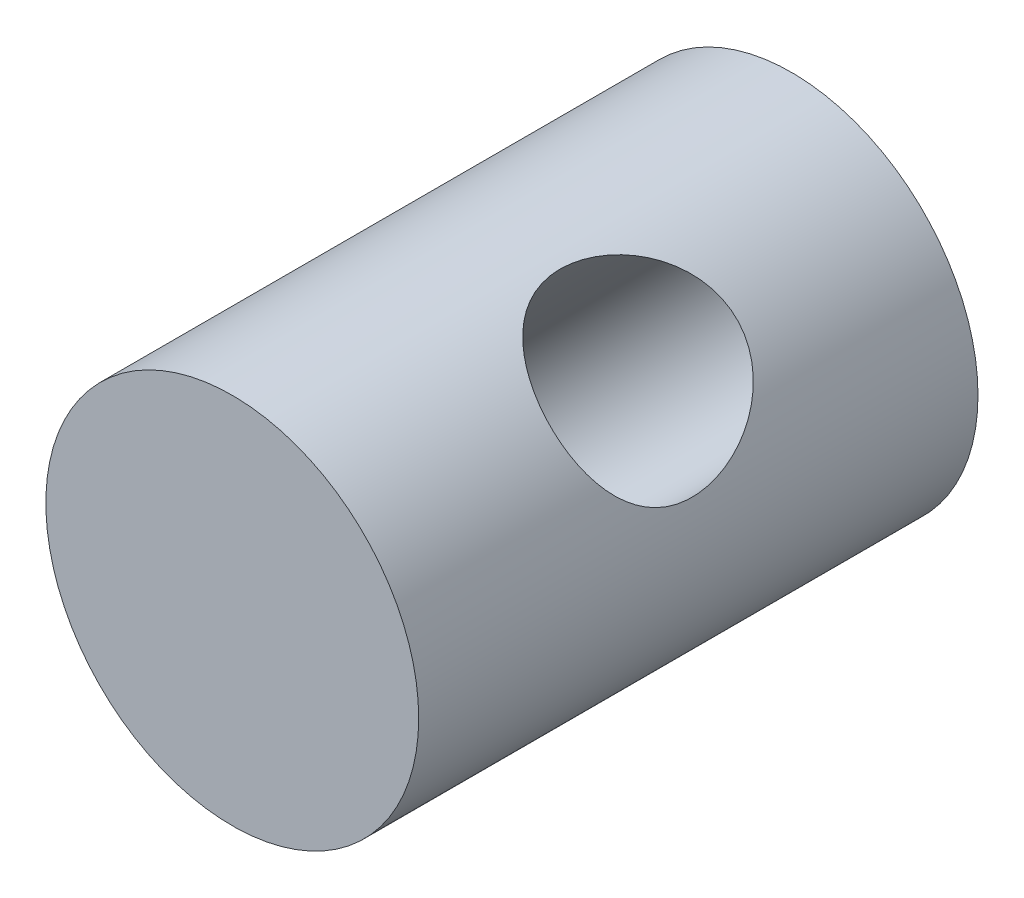
SolidWorks part; units mm, degrees
ref_plane "Front Plane" through (0, 0, 0) normal (0, 0, 1) x (1, 0, 0)
ref_plane "Top Plane" through (0, 0, 0) normal (0, 1, 0) x (1, 0, 0)
ref_plane "Right Plane" through (0, 0, 0) normal (1, 0, 0) x (0, 0, -1)
sketch "Sketch1" plane through (0, 0, 0) normal (0, 0, 1) x (1, 0, 0)
  line L0 (0, 0) -> (2.8284, 2.8284) construction
  circle A0 centre (0, 0) radius 4
extrude "Boss-Extrude1" add sketch "Sketch1" along normal blind 12
ref_plane "Plane1" through (2.8284, 2.8284, 0) normal (0.7071, 0.7071, 0) x (0.7071, -0.7071, 0)
sketch "Sketch2" plane through (2.8284, 2.8284, 0) normal (0.7071, 0.7071, 0) x (0.7071, -0.7071, 0)
  line L0 (-4, 0) -> (4, 0) construction
  circle A0 centre (0, -6) radius 2
  dimension "D1" = 6
extrude "Cut-Extrude1" cut sketch "Sketch2" against normal through all
